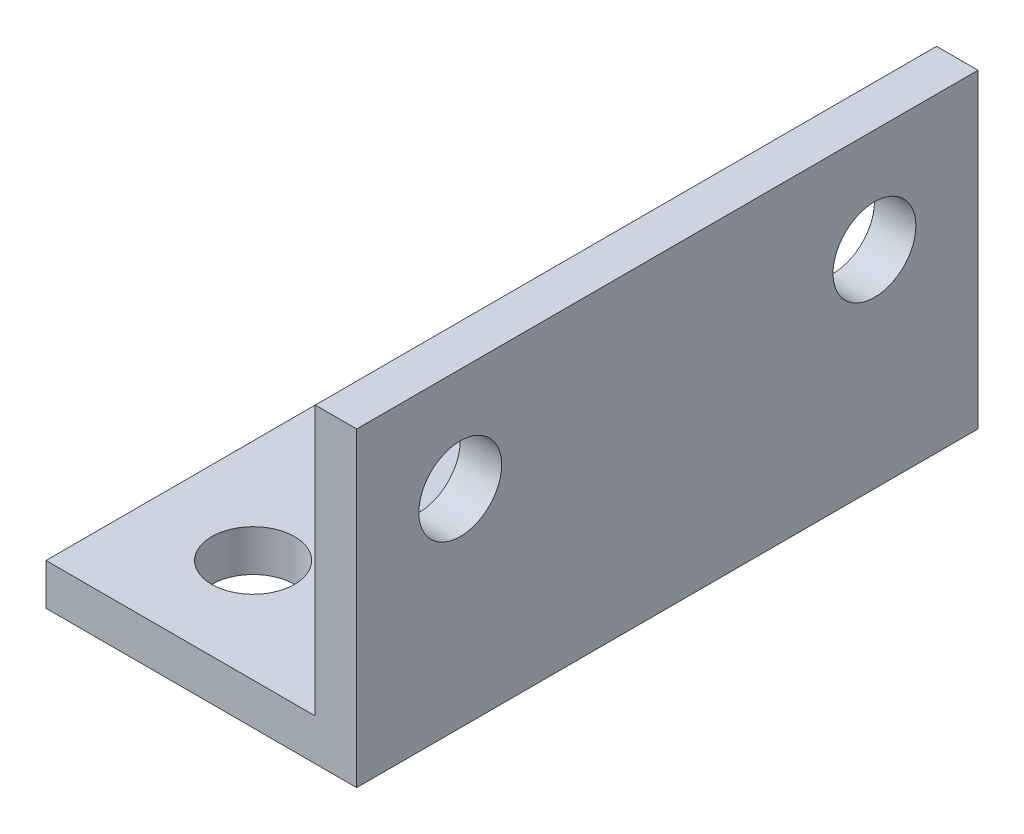
SolidWorks part; units mm, degrees
material "Alloy Steel (SS)"
ref_plane "Front Plane" through (0, 0, 0) normal (0, 0, 1) x (1, 0, 0)
ref_plane "Top Plane" through (0, 0, 0) normal (0, 1, 0) x (1, 0, 0)
ref_plane "Right Plane" through (0, 0, 0) normal (1, 0, 0) x (0, 0, -1)
sketch "Sketch1" plane through (0, 0, 0) normal (0, 0, 1) x (1, 0, 0)
  line L0 (0, 15) -> (0, 0)
  line L1 (0, 0) -> (-15, 0)
  line L2 (-2, 15) -> (-2, 2)
  line L3 (-2, 2) -> (-15, 2)
  line L4 (-2, 15) -> (0, 15)
  line L5 (-15, 2) -> (-15, 0)
  dimension "D1" = 15
  dimension "D2" = 15
  dimension "D3" = 2
extrude "Boss-Extrude1" add sketch "Sketch1" along normal blind 30
sketch "Sketch2" plane through (0, 0, 0) normal (1, 0, 0) x (0, 0, -1)
  line L0 (-30, 0) -> (0, 0) construction
  line L1 (-15, 0) -> (-15, 15) construction
  line L2 (-30, 15) -> (0, 15) construction
  circle A0 centre (-25, 10) radius 2
  circle A1 centre (-5, 10) radius 2
  dimension "D3" = 10
  dimension "5" = 4
  dimension "D1" = 10
  dimension "D2" = 10
extrude "Cut-Extrude1" cut sketch "Sketch2" against normal up to next
sketch "Sketch3" plane through (0, 2, 0) normal (0, 1, 0) x (1, 0, 0)
  line L0 (-15, -15) -> (-2, -15) construction
  line L1 (-15, -30) -> (-15, 0) construction
  line L2 (-2, -30) -> (-2, 0) construction
  line L3 (0, -30) -> (0, 0) construction
  circle A0 centre (-10, -5) radius 2
  circle A1 centre (-10, -25) radius 2
  dimension "D1" = 4
  dimension "D2" = 10
  dimension "D3" = 10
  dimension "D4" = 10
extrude "Cut-Extrude2" cut sketch "Sketch3" against normal up to next
